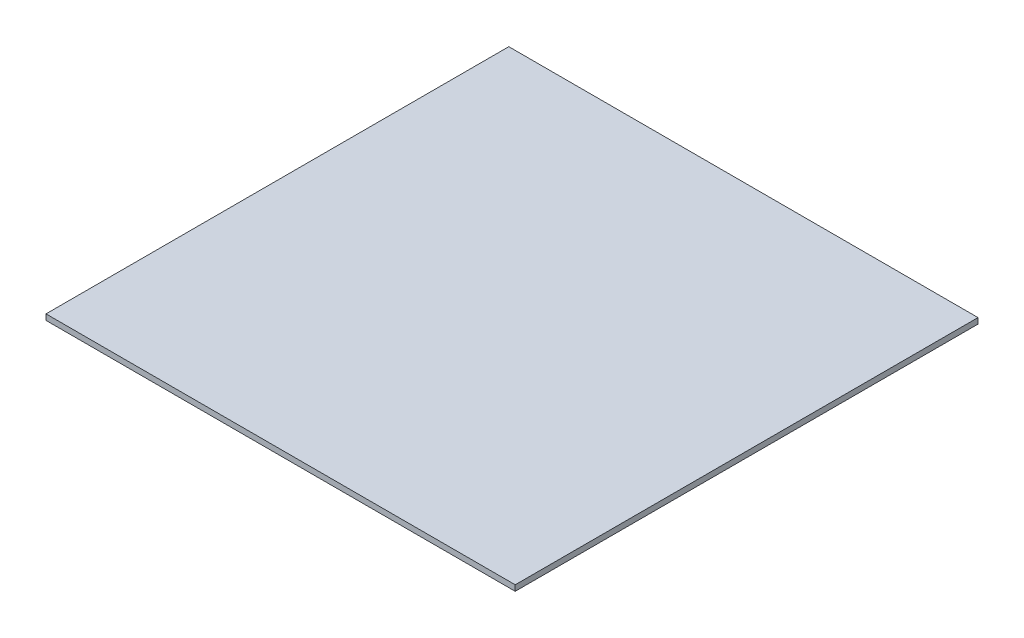
SolidWorks part; units mm, degrees
ref_plane "Front Plane" through (0, 0, 0) normal (0, 0, 1) x (1, 0, 0)
ref_plane "Top Plane" through (0, 0, 0) normal (0, 1, 0) x (1, 0, 0)
ref_plane "Right Plane" through (0, 0, 0) normal (1, 0, 0) x (0, 0, -1)
sketch "Sketch1" plane through (0, 0, 0) normal (0, 1, 0) x (1, 0, 0)
  line L1 (-492.125, -485.394) -> (492.125, -485.394)
  line L2 (-492.125, -485.394) -> (-492.125, 485.394)
  line L3 (-492.125, 485.394) -> (492.125, 485.394)
  line L4 (492.125, -485.394) -> (492.125, 485.394)
  line L5 (-492.125, -485.394) -> (492.125, 485.394) construction
  line L6 (-492.125, 485.394) -> (492.125, -485.394) construction
  point P0 (0, 0)
  dimension "D1" = 984.25
  dimension "D2" = 970.788
extrude "Boss-Extrude1" add sketch "Sketch1" along normal blind 11.938
